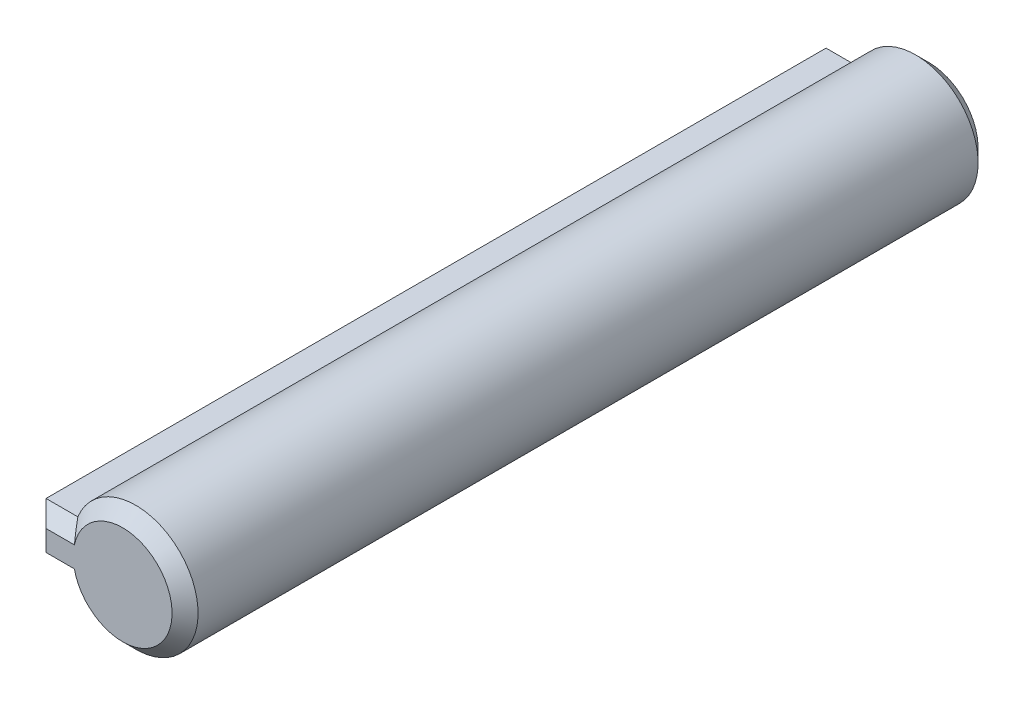
SolidWorks part; units mm, degrees
ref_plane "Front Plane" through (0, 0, 0) normal (1, 0, 0) x (0, 1, 0)
ref_plane "Top Plane" through (0, 0, 0) normal (0, 0, 1) x (0, 1, 0)
ref_plane "Right Plane" through (0, 0, 0) normal (0, 1, 0) x (-1, 0, 0)
sketch "Sketch1" plane through (0, 0, 0) normal (0, 0, 1) x (0, 1, 0)
  line L1 (-1.8, 6.8976) -> (1.8, 6.8976)
  line L2 (-1.8, 6.8976) -> (-1.8, 1.6976)
  line L3 (-1.8, 1.6976) -> (1.8, 1.6976)
  line L4 (1.8, 6.8976) -> (1.8, 1.6976)
  circle A0 centre (0, 0) radius 4.8
  point P7 (0, 1.6976)
  point P8 (-1.8, 4.2976)
  dimension "D1" = 9.6
  dimension "D2" = 3.6
  dimension "D3" = 2.6
extrude "Boss-Extrude1" add sketch "Sketch1" along normal blind 62 contours A0 L4 L1 L2 | L2 A0 L4 L3 | L4 A0 L2 L3
chamfer "Chamfer1" distance 1 angle 45 4 edges at (-6.8976, 0, 62) (-5.6736, 1.8, 62) (4.8, 0, 62) (-5.6736, -1.8, 62)
chamfer "Chamfer2" distance 1 angle 45 4 edges at (-5.6736, -1.8, 0) (-6.8976, 0, 0) (-5.6736, 1.8, 0) (4.8, 0, 0)
scale "Scale1" scale about centroid uniform scaling yes scale factor 0.75
scale "Scale2" scale about centroid uniform scaling yes scale factor 0.85
